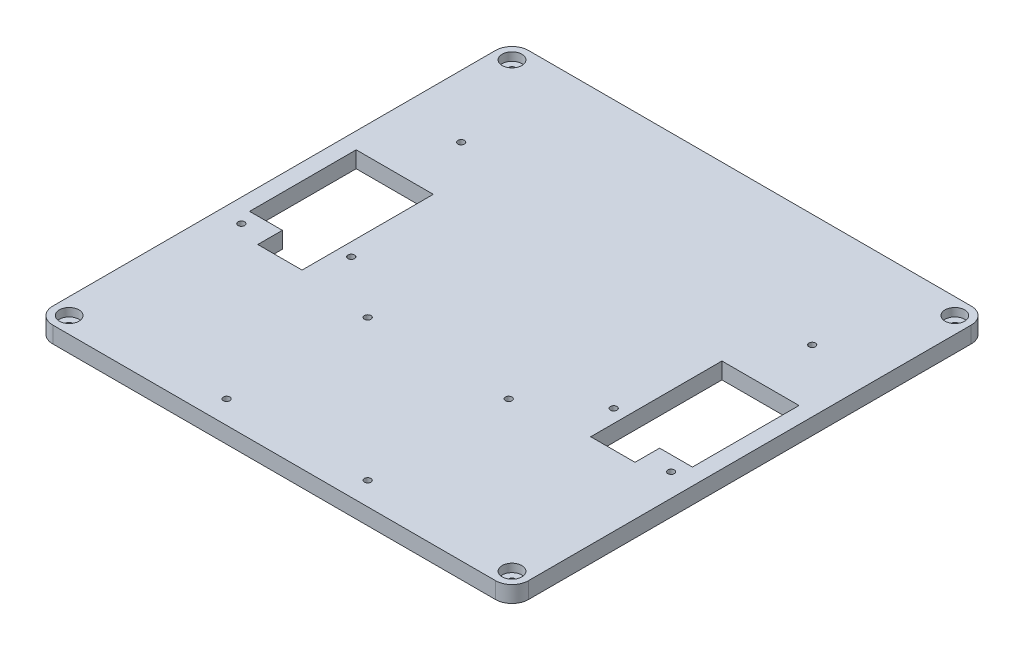
SolidWorks part; units mm, degrees
material "Acrylique (impact moyen-haut)"
ref_plane "Plan de face" through (0, 0, 0) normal (0, 0, 1) x (1, 0, 0)
ref_plane "Plan de dessus" through (0, 0, 0) normal (0, 1, 0) x (1, 0, 0)
ref_plane "Plan de droite" through (0, 0, 0) normal (1, 0, 0) x (0, 0, -1)
sketch "Esquisse2" plane through (0, 0, 0) normal (0, 1, 0) x (1, 0, 0)
  line L0 (145, 290) -> (145, 0) construction
  line L1 (0, 0) -> (290, 0)
  line L2 (0, 0) -> (0, 290)
  line L3 (0, 290) -> (290, 290)
  line L4 (290, 0) -> (290, 290)
  line L5 (0, 145) -> (290, 145) construction
  line L6 (233, 185) -> (233, 145)
  line L7 (233, 145) -> (233, 105)
  line L8 (233, 105) -> (260, 105)
  line L9 (260, 105) -> (260, 120)
  line L10 (260, 120) -> (280, 120)
  line L11 (280, 120) -> (280, 185)
  line L12 (280, 185) -> (233, 185)
  line L13 (30, 105) -> (30, 120)
  line L14 (57, 145) -> (57, 105)
  line L15 (57, 105) -> (30, 105)
  line L16 (30, 120) -> (10, 120)
  line L17 (10, 120) -> (10, 185)
  line L18 (57, 185) -> (57, 145)
  line L19 (10, 185) -> (57, 185)
  line L20 (233, 111) -> (284.7415, 111) construction
  line L21 (276, 120) -> (276, 111) construction
  line L22 (225, 193.2692) -> (225, 93.0015) construction
  circle A0 centre (276, 111) radius 2
  circle A1 centre (225, 127) radius 2
  circle A2 centre (252, 221) radius 2
  circle A3 centre (14, 111) radius 2
  circle A4 centre (65, 127) radius 2
  circle A5 centre (38, 221) radius 2
  dimension "D10" = 4
  dimension "D13" = 4
  dimension "D16" = 4
  dimension "D1" = 290
  dimension "D2" = 290
  dimension "D3" = 80
  dimension "D4" = 65
  dimension "D5" = 27
  dimension "D6" = 20
  dimension "D7" = 10
  dimension "D8" = 43
  dimension "D9" = 74
  dimension "D11" = 8
  dimension "D12" = 22
  dimension "D14" = 36
  dimension "D15" = 19
extrude "Boss.-Extru.1" add sketch "Esquisse2" along normal blind 10
sketch "Esquisse3" plane through (0, 10, 0) normal (0, 1, 0) x (1, 0, 0)
  line L0 (0, 145) -> (290, 145) construction
  line L1 (0, 290) -> (0, 0) construction
  line L2 (290, 0) -> (290, 290) construction
  line L3 (145, 290) -> (145, 0) construction
  line L4 (290, 290) -> (0, 290) construction
  line L5 (0, 0) -> (290, 0) construction
  line L6 (0, 280) -> (10, 280) construction
  line L7 (10, 280) -> (10, 290) construction
  circle A0 centre (10, 280) radius 2
  circle A1 centre (280, 280) radius 2
  circle A2 centre (280, 10) radius 2
  circle A3 centre (10, 10) radius 2
  dimension "D3" = 4
  dimension "D1" = 10
  dimension "D2" = 10
extrude "Enlèv. mat.-Extru.1" cut sketch "Esquisse3" against normal blind 10
fillet "Congé1" radius 10 4 edges at (0, 5, -290) (0, 5, 0) (290, 5, 0) (290, 5, -290)
sketch "Esquisse4" plane through (0, 10, 0) normal (0, 1, 0) x (1, 0, 0)
  circle A0 centre (10, 280) radius 6
  circle A1 centre (280, 280) radius 6
  circle A2 centre (280, 10) radius 6
  circle A3 centre (10, 10) radius 6
  dimension "D1" = 12
extrude "Enlèv. mat.-Extru.2" cut sketch "Esquisse4" against normal blind 5
sketch "Esquisse5" plane through (0, 0, 0) normal (0, -1, 0) x (1, 0, 0)
  circle A0 centre (102, -14) radius 2
  circle A1 centre (188, -14) radius 2
  circle A2 centre (188, -100) radius 2
  circle A3 centre (102, -100) radius 2
extrude "Enlèv. mat.-Extru.3" cut sketch "Esquisse5" against normal blind 10
